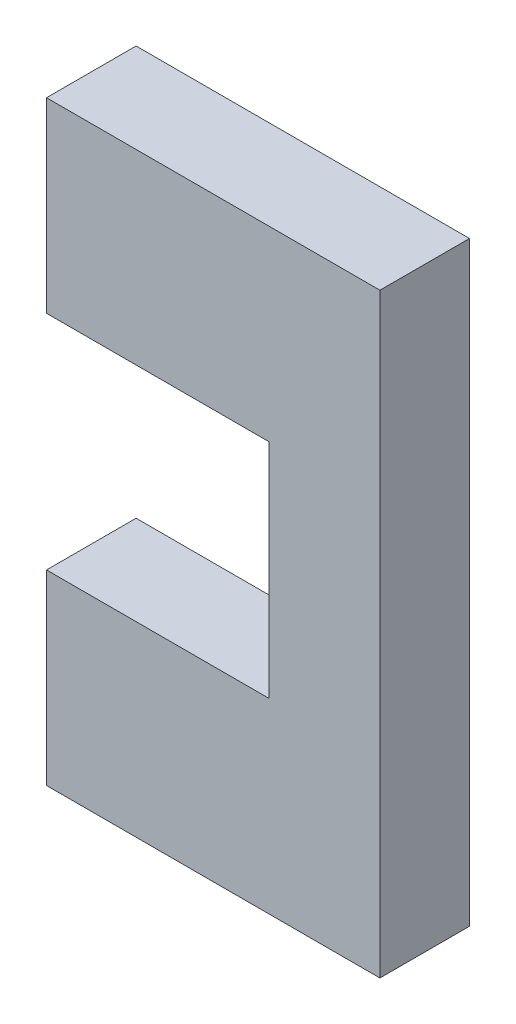
SolidWorks part; units mm, degrees
ref_plane "Front" through (0, 0, 0) normal (0, 0, 1) x (1, 0, 0)
ref_plane "Top" through (0, 0, 0) normal (0, 1, 0) x (1, 0, 0)
ref_plane "Right" through (0, 0, 0) normal (1, 0, 0) x (0, 0, -1)
sketch "Sketch1" plane through (0, 0, 0) normal (0, 0, 1) x (1, 0, 0)
  line L13 (38.1, 215.218) -> (38.1, 193.882)
  line L14 (38.1, 193.882) -> (63.5, 193.882)
  line L15 (63.5, 193.882) -> (63.5, 168.482)
  line L16 (63.5, 168.482) -> (38.1, 168.482)
  line L17 (38.1, 168.482) -> (38.1, 147.146)
  line L18 (38.1, 147.146) -> (76.2, 147.146)
  line L19 (76.2, 147.146) -> (76.2, 215.218)
  line L20 (76.2, 215.218) -> (38.1, 215.218)
  line L21 (50.8, 204.55) -> (50.8, 157.814) construction
  line L22 (50.8, 204.55) -> (50.8, 157.814) construction
  point P10 (0, 0)
  point P11 (38.1, 204.55)
  point P13 (0, 0)
  point P14 (38.1, 157.814)
  point P15 (0, 0)
  dimension "D1" = 12.7
  dimension "D2" = 25.4
  dimension "D3" = 25.4
  dimension "D4" = 12.7
extrude "Boss-Extrude2" add sketch "Sketch1" along normal up to surface (10.2372 mm away)
